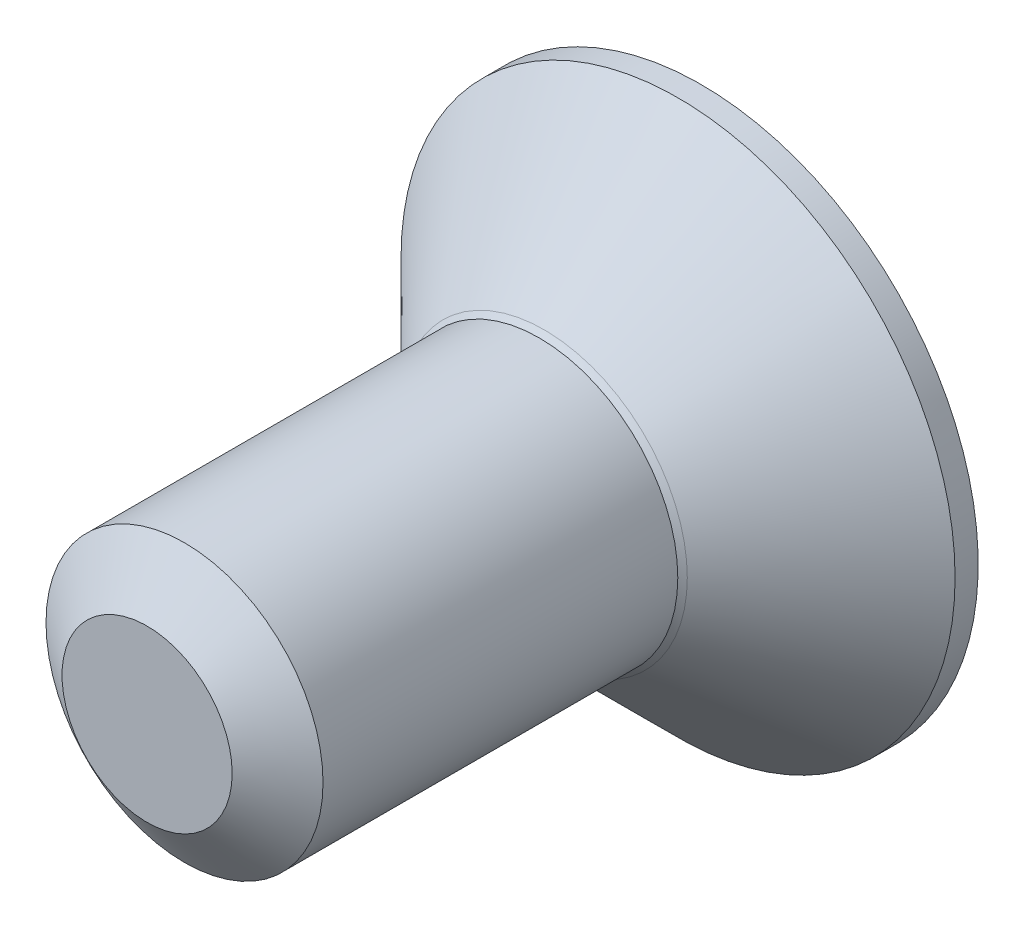
SolidWorks part; units mm, degrees
material "Ti-6Al-4VSolution treated and aged (SS)"
ref_plane "Front Plane" through (0, 0, 0) normal (0, 0, 1) x (1, 0, 0)
ref_plane "Top Plane" through (0, 0, 0) normal (0, 1, 0) x (1, 0, 0)
ref_plane "Right Plane" through (0, 0, 0) normal (1, 0, 0) x (0, 0, -1)
sketch "Sketch1" plane through (0, 0, 0) normal (0, 0, 1) x (1, 0, 0)
  circle A0 centre (0, 0) radius 1.5
  dimension "OD" = 3
extrude "Extrude1" add sketch "Sketch1" against normal blind 6
sketch "Sketch2" plane through (0, 0, 0) normal (0, 0, 1) x (1, 0, 0)
  circle A0 centre (0, 0) radius 1.5 construction
  circle A1 centre (0, 0) radius 1.5
curve "Helix/Spiral1" pitch 0.5 height 6.5 turns 13 parameters "pitch"=0.5
sketch "Sketch3" plane through (0, 0, 0) normal (1, 0, 0) x (0, 0, -1)
  line L0 (-0.4375, 1.5) -> (-0.25, 1.1752)
  line L1 (-0.25, 1.1752) -> (-0.1875, 1.1752)
  line L2 (-0.1875, 1.1752) -> (0, 1.5)
  line L3 (-0.4375, 1.5) -> (0, 1.5)
  line L4 (-0.2188, 1.5) -> (-0.2188, 1.1752) construction
  line L5 (-0.3438, 1.3376) -> (-0.0937, 1.3376) construction
  line L6 (0, 1.5) -> (0, -1.5) construction
  dimension "D1" = 0.0625
  dimension "D2" = 0.25
  dimension "D3" = 60
sketch "Sketch4" plane through (0, 0, 0) normal (1, 0, 0) x (0, 0, -1)
  line L0 (0.4053, 1.5) -> (0, 0.9212)
  line L1 (0, 0.9212) -> (0, 1.5)
  line L2 (0.4053, 1.5) -> (0, 1.5)
  line L3 (-0.4375, 1.5) -> (0, 1.5) construction
  line L4 (0, 0) -> (7.0209, 0) construction
  dimension "D1" = 55
  dimension "D2" = 0.254
revolve "Cut-Revolve1" cut sketch "Sketch4" angle 360 about L4
sketch "Sketch5" [suppressed] plane through (0, 0, 0) normal (1, 0, 0) x (0, 0, -1)
  line L0 (6, -1.1822) -> (6, 1.0703) construction
  line L1 (6, 1.55) -> (18.1906, 1.55)
  line L2 (6, 1.55) -> (6, 0)
  line L3 (6, 0) -> (18, 0)
  line L4 (18, 1.2198) -> (18, 0)
  line L5 (18.1906, 1.55) -> (18, 1.2198)
  line L6 (0, 0) -> (9.9695, 0) construction
  point P3 (18, 1.55)
  point P10 (18, 1.55)
  dimension "D1" = 0.3302
  dimension "Thread min" = 18
  dimension "D2" = 0.05
  dimension "D3" = 30
revolve "partially thread" [suppressed] add sketch "Sketch5" angle 360 about L6
sketch "Sketch6" plane through (0, 0, -6) normal (0, 0, -1) x (-1, 0, 0)
  circle A0 centre (0, 0) radius 3
  dimension "head dia" = 6
extrude "Extrude2" add sketch "Sketch6" against normal blind 1.7
sketch "Sketch10" plane through (0, 0, 0) normal (1, 0, 0) x (0, 0, -1)
  line L0 (5.75, -3) -> (4.3, -1.55)
  line L1 (4.3, -1.55) -> (4.3, -3)
  line L2 (5.75, -3) -> (4.3, -3)
  line L3 (0, 0) -> (4.3, 0) construction
  line L4 (4.3, 3) -> (4.3, -3) construction
  line L5 (5.75, 3) -> (4.3, 3) construction
  line L6 (4.3, 1.55) -> (4.3, 3) construction
  line L7 (5.75, 3) -> (4.3, 1.55) construction
  line L8 (4.3, 3) -> (4.3, -3) construction
  line L9 (4.3, 1.55) -> (4.3, -1.55) construction
  dimension "D1" = 45
  dimension "D2" = 0.05
revolve "Cut-Revolve2" cut sketch "Sketch10" angle 360 about L3
sketch "Sketch11" plane through (0, 0, 0) normal (1, 0, 0) x (0, 0, -1)
  line L0 (-0.25, 1.1752) -> (-0.1875, 1.1752) construction
  line L1 (5.75, 3) -> (4.3, 1.55) construction
  line L2 (3.3953, 1.1752) -> (3.3953, 0)
  line L3 (3.3953, 0) -> (4.3, 0)
  line L4 (4.3, 1.55) -> (4.3, 0)
  line L5 (0, 0) -> (4.3, 0) construction
  arc A0 (4.3, 1.55) -> (3.3953, 1.1752) centre (3.3953, 2.4547) cw
revolve "Revolve1" add sketch "Sketch11" angle 360 about L3
sketch "Sketch7" plane through (0, 0, -6) normal (0, 0, 1) x (1, 0, 0)
  line L1 (0, 1.1547) -> (-1, 0.5774)
  line L2 (-1, 0.5774) -> (-1, -0.5774)
  line L3 (-1, -0.5774) -> (0, -1.1547)
  line L4 (0, -1.1547) -> (1, -0.5774)
  line L5 (1, -0.5774) -> (1, 0.5774)
  line L6 (1, 0.5774) -> (0, 1.1547)
  circle A0 centre (0, 0) radius 1 construction
  dimension "hex dia" = 2
extrude "Cut-Extrude1" cut sketch "Sketch7" along normal blind 1.5
sketch "Sketch8" plane through (0, 0, -6) normal (0, 0, 1) x (1, 0, 0)
  circle A0 centre (0, 0) radius 1.1547
extrude "Cut-Extrude2" cut sketch "Sketch8" along normal through all draft 45
sketch "Sketch9" plane through (0, 0, 0) normal (1, 0, 0) x (0, 0, -1)
  line L0 (0, 1.5) -> (0, -1.5) construction
  line L1 (2.75, 1.5) -> (2.75, -1.5) construction
  line L2 (4.3, 1.5) -> (4.3, -1.5) construction
  line L3 (4.3, -1.55) -> (4.3, -3) construction
  dimension "D1" = 2.75
equation "\"D3@Helix/Spiral1\" = \"screw length@Extrude1\"+\"pitch@Helix/Spiral1\""
equation "\"D1@Sketch3\" = \"pitch@Helix/Spiral1\"*.125"
equation "\"D2@Sketch3\" = \"pitch@Helix/Spiral1\"*.5"
equation "\"D1@Cut-Extrude1\" = \"hex dia@Sketch7\"*.75"
equation "\"D1@Sketch9\" = \"pitch@Helix/Spiral1\"*5.5"
equation "\"D2@Sketch10\" = \"D2@Sketch5\""
